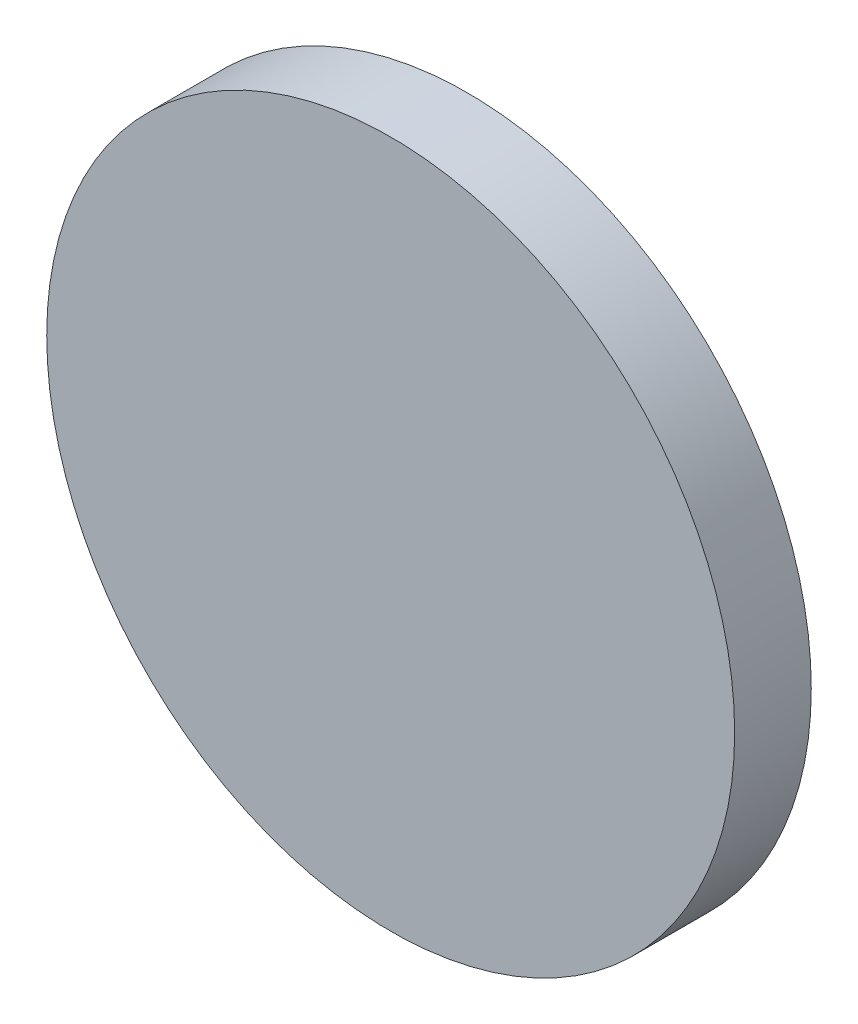
SolidWorks part; units mm, degrees
ref_plane "Front Plane" through (0, 0, 0) normal (0, 0, 1) x (1, 0, 0)
ref_plane "Top Plane" through (0, 0, 0) normal (0, 1, 0) x (1, 0, 0)
ref_plane "Right Plane" through (0, 0, 0) normal (1, 0, 0) x (0, 0, -1)
sketch "Sketch2" plane through (0, 0, 0) normal (0, 0, 1) x (1, 0, 0)
  circle A0 centre (0, 0) radius 44.9
  dimension "D1" = 89.8
extrude "Boss-Extrude1" add sketch "Sketch2" along normal blind 10
